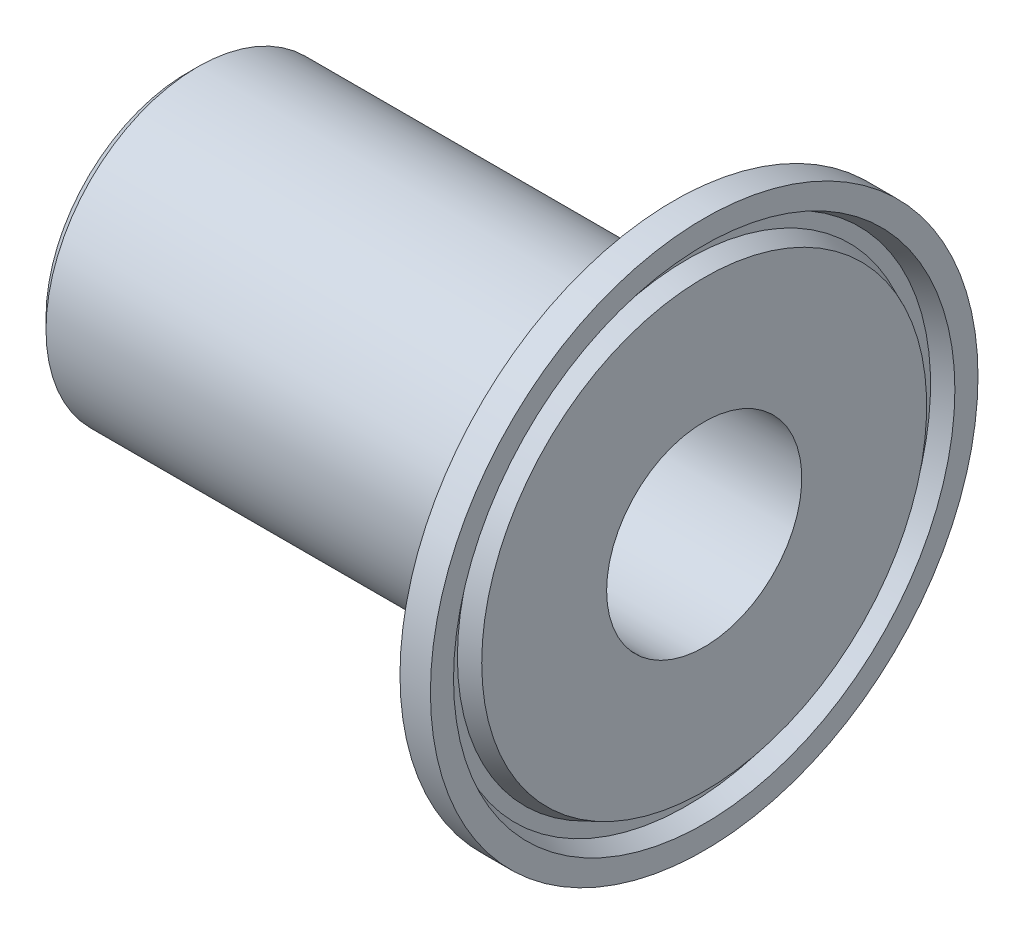
SolidWorks part; units mm, degrees
material "6061 Alloy"
ref_plane "Front Plane" through (0, 0, 0) normal (0, 0, 1) x (1, 0, 0)
ref_plane "Top Plane" through (0, 0, 0) normal (0, 1, 0) x (1, 0, 0)
ref_plane "Right Plane" through (0, 0, 0) normal (1, 0, 0) x (0, 0, -1)
sketch "Sketch1" plane through (0, 0, 0) normal (0, 0, 1) x (1, 0, 0)
  line L4 (41.0741, 14.7521) -> (44.895, 25.25)
  line L5 (44.895, 25.25) -> (47.7017, 25.25)
  line L6 (47.7017, 25.25) -> (47.7017, 23.1186)
  line L7 (47.7017, 9) -> (0, 9)
  line L8 (0, 0) -> (52.6945, 0) construction
  line L9 (0, 9) -> (0, 0) construction
  line L10 (47.7017, 23.1186) -> (46.1269, 22.4501)
  line L11 (46.1269, 22.4501) -> (46.1269, 21.1871)
  line L12 (46.1269, 21.1871) -> (47.7017, 20.5186)
  line L13 (46.1269, 21.8186) -> (47.7017, 21.8186) construction
  line L14 (47.7017, 20.5186) -> (47.7017, 9)
  line L15 (0, 14) -> (0, 9)
  line L16 (40, 14) -> (0, 14)
  arc A0 (40, 14) -> (41.0741, 14.7521) centre (40, 15.143) ccw
  circle A1 centre (47.7017, 21.8186) radius 1.15 construction
  point P16 (40, 14)
  dimension "D9" = 1.143
  dimension "D14" = 2.3
  dimension "D1" = 20
  dimension "D2" = 25.25
  dimension "D3" = 2.8067
  dimension "D4" = 28
  dimension "D5" = 5
  dimension "D7" = 40
  dimension "D10" = 46
  dimension "D11" = 21.8186
  dimension "D12" = 1.5748
  dimension "D13" = 2.6
revolve "Revolve1" add sketch "Sketch1" angle 360 about L8
fillet "Fillet1" [suppressed] radius 1.1938
fillet "Fillet2" [suppressed] radius 0.7874
chamfer "Chamfer1" [suppressed] distance 2
ref_plane "Plane1" through (0, 0, -14) normal (0, 0, -1) x (-1, 0, 0)
chamfer "Chamfer3" distance 1 angle 45 1 edges at (0, 0, 14)
